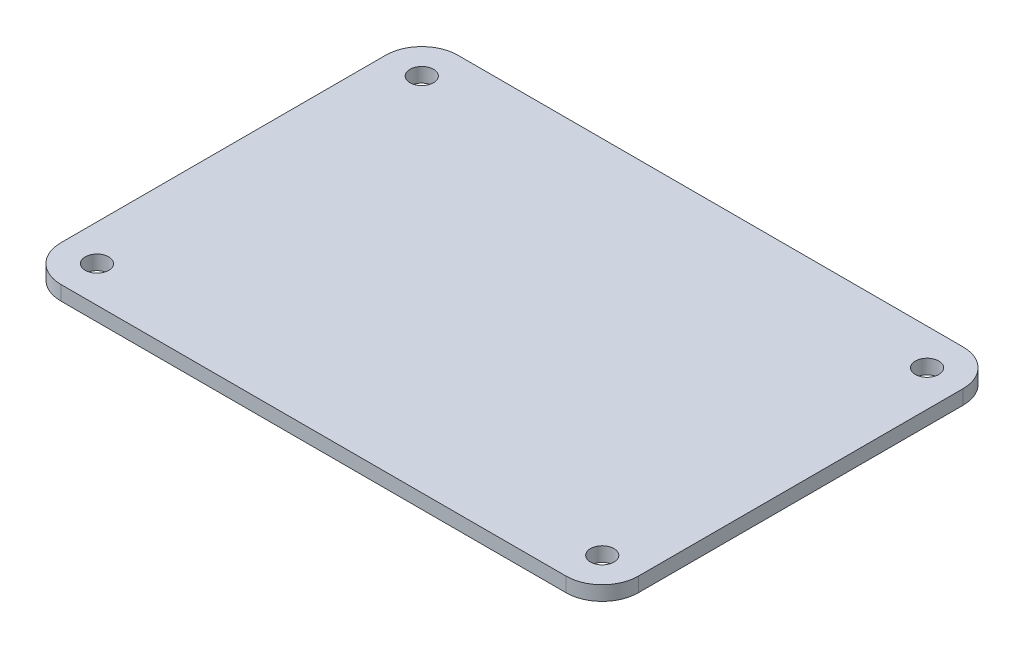
SolidWorks part; units mm, degrees
material "ABS"
ref_plane "Спереди" through (0, 0, 0) normal (0, 0, 1) x (1, 0, 0)
ref_plane "Сверху" through (0, 0, 0) normal (0, 1, 0) x (1, 0, 0)
ref_plane "Справа" through (0, 0, 0) normal (1, 0, 0) x (0, 0, -1)
sketch "Эскиз1" plane through (0, 0, 0) normal (0, 1, 0) x (1, 0, 0)
  line L0 (0, 0) -> (-95.7217, 0) construction
  line L1 (70, -55) -> (-70, -55)
  line L2 (80, -45) -> (80, 45)
  line L3 (70, 55) -> (-70, 55)
  line L4 (-80, -45) -> (-80, 45)
  line L5 (80, -55) -> (-80, 55) construction
  line L6 (80, 55) -> (-80, -55) construction
  line L7 (0, 0) -> (0, 74.6381) construction
  line L8 (-60, 0) -> (-73.6976, 13.6976) construction
  arc A11 (-80, -45) -> (-70, -55) centre (-70, -45) ccw
  arc A12 (70, -55) -> (80, -45) centre (70, -45) ccw
  arc A13 (80, 45) -> (70, 55) centre (70, 45) ccw
  arc A14 (-70, 55) -> (-80, 45) centre (-70, 45) ccw
  circle A15 centre (-70, 45) radius 3.25
  circle A16 centre (-70, -45) radius 3.25
  circle A17 centre (70, -45) radius 3.25
  circle A18 centre (70, 45) radius 3.25
  point P0 (0, 0)
  point P24 (-60, 0)
  dimension "D8" = 10
  dimension "D9" = 6.5
  dimension "D1" = 110
  dimension "D2" = 160
  dimension "D3" = 20
extrude "Бобышка-Вытянуть1" add sketch "Эскиз1" along normal blind 4
